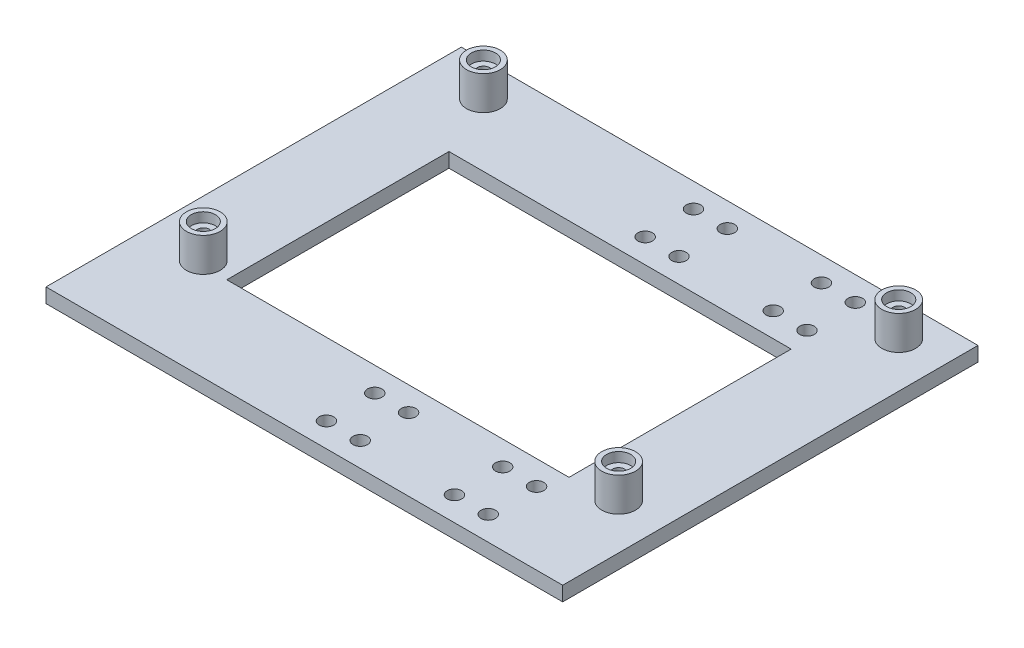
SolidWorks part; units mm, degrees
ref_plane "Front Plane" through (0, 0, 0) normal (0, 0, 1) x (1, 0, 0)
ref_plane "Top Plane" through (0, 0, 0) normal (0, 1, 0) x (1, 0, 0)
ref_plane "Right Plane" through (0, 0, 0) normal (1, 0, 0) x (0, 0, -1)
sketch "Sketch1" plane through (0, 0, 0) normal (0, 1, 0) x (1, 0, 0)
  line L0 (0, 0) -> (0, 28)
  line L1 (0, 28) -> (0, -28)
  line L2 (0, 28) -> (-7, 28)
  line L3 (-7, 28) -> (-7, 38)
  line L4 (-7, 38) -> (0, 38)
  line L5 (0, -28) -> (-7, -28)
  line L6 (-7, -28) -> (-7, -38)
  line L7 (-7, -38) -> (0, -38)
  line L8 (-7, 38) -> (-26.5, 38)
  line L9 (-26.5, 38) -> (-26.5, 28)
  line L10 (-26.5, 28) -> (-33.5, 28)
  line L11 (-33.5, 28) -> (-33.5, 38)
  line L12 (-26.5, 28) -> (-26.5, -28)
  line L13 (-26.5, -28) -> (-33.5, -28)
  line L14 (-33.5, -28) -> (-33.5, -38)
  line L15 (-33.5, -38) -> (-26.5, -38)
  line L16 (-26.5, 38) -> (-26.5, 43)
  line L17 (-26.5, -38) -> (-26.5, -43)
  line L18 (-26.5, 43) -> (-120.0285, 43)
  line L19 (-120.0285, 43) -> (61.4662, 43)
  line L20 (0, 28) -> (11, 28)
  line L21 (11, 43) -> (11, 36)
  line L22 (11, 36) -> (-75, 36)
  line L23 (-75, 36) -> (-75, -22)
  line L24 (-75, -22) -> (11, -22)
  line L25 (0, -38) -> (0, -43)
  line L26 (20.4124, 43) -> (20.4124, -43)
  line L27 (20.4124, -43) -> (-86.573, -43)
  line L28 (-86.573, -43) -> (-86.573, 43)
  line L29 (-33.5, 28) -> (-33.5, 23)
  line L30 (-33.5, -28) -> (-33.5, -23)
  line L31 (-33.5, 23) -> (-69.1314, 23)
  line L32 (-69.1314, 23) -> (-69.1314, -23)
  line L33 (-69.1314, -23) -> (1.725, -23)
  line L34 (1.725, -23) -> (1.725, 23)
  line L35 (1.725, 23) -> (-33.5, 23)
  circle A0 centre (-33.5, 38) radius 1.5
  circle A1 centre (-33.5, 28) radius 1.5
  circle A2 centre (-26.5, 28) radius 1.5
  circle A3 centre (-26.5, 38) radius 1.5
  circle A4 centre (-7, 38) radius 1.5
  circle A5 centre (-7, 28) radius 1.5
  circle A6 centre (0, 28) radius 1.5
  circle A7 centre (0, 38) radius 1.5
  circle A8 centre (-33.5, -28) radius 1.5
  circle A9 centre (-26.5, -28) radius 1.5
  circle A10 centre (-26.5, -38) radius 1.5
  circle A11 centre (-33.5, -38) radius 1.5
  circle A12 centre (-7, -38) radius 1.5
  circle A13 centre (-7, -28) radius 1.5
  circle A14 centre (0, -28) radius 1.5
  circle A15 centre (0, -38) radius 1.5
  circle A16 centre (-75, 36) radius 3.5
  circle A17 centre (11, 36) radius 3.5
  circle A18 centre (11, -22) radius 3.5
  circle A19 centre (-75, -22) radius 3.5
extrude "Boss-Extrude1" add sketch "Sketch1" along normal blind 3
sketch "Sketch3" plane through (0, 3, 0) normal (0, 1, 0) x (1, 0, 0)
  circle A0 centre (-75, -22) radius 3.5 construction
  circle A1 centre (11, -22) radius 3.5 construction
  circle A2 centre (11, 36) radius 3.5 construction
  circle A3 centre (-75, 36) radius 3.5 construction
  circle A4 centre (-75, -22) radius 3.5
  circle A5 centre (11, -22) radius 3.5
  circle A6 centre (11, 36) radius 3.5
  circle A7 centre (-75, 36) radius 3.5
extrude "Boss-Extrude2" add sketch "Sketch3" along normal blind 7 separate body
sketch "Sketch4" plane through (0, 3, 0) normal (0, -1, 0) x (1, 0, 0)
  circle A0 centre (-75, -36) radius 3.5 construction
  circle A1 centre (11, -36) radius 3.5 construction
  circle A2 centre (11, 22) radius 3.5 construction
  circle A3 centre (-75, 22) radius 3.5 construction
  circle A4 centre (-75, -36) radius 3.5
  circle A5 centre (11, -36) radius 3.5
  circle A6 centre (11, 22) radius 3.5
  circle A7 centre (-75, 22) radius 3.5
extrude "Boss-Extrude3" add sketch "Sketch4" along normal up to surface (3 mm away) up to face at (-7, 0, -26.5)
sketch "Sketch5" plane through (0, 10, 0) normal (0, 1, 0) x (1, 0, 0)
  circle A0 centre (-75, 36) radius 3.5 construction
  circle A1 centre (11, -22) radius 3.5 construction
  circle A2 centre (-75, -22) radius 3.5 construction
  circle A3 centre (11, -22) radius 3.5 construction
  circle A4 centre (11, 36) radius 3.5 construction
  circle A5 centre (-75, 36) radius 3.5
  circle A6 centre (11, -22) radius 3.5
  circle A7 centre (-75, -22) radius 3.5
  circle A8 centre (11, -22) radius 3.5
  circle A9 centre (11, 36) radius 3.5
  circle A10 centre (-75, 36) radius 1.25
  circle A11 centre (11, 36) radius 1.25
  circle A12 centre (11, -22) radius 1.25
  circle A13 centre (-75, -22) radius 1.25
extrude "Cut-Extrude1" cut sketch "Sketch5" against normal blind 7 contours A11 | A12 | A13 | A10
sketch "Sketch6" plane through (0, 10, 0) normal (0, 1, 0) x (1, 0, 0)
  circle A0 centre (-75, 36) radius 2.5
  circle A1 centre (11, 36) radius 2.5
  circle A2 centre (-75, -22) radius 2.5
  circle A3 centre (11, -22) radius 2.5
extrude "Cut-Extrude2" cut sketch "Sketch6" against normal blind 2
